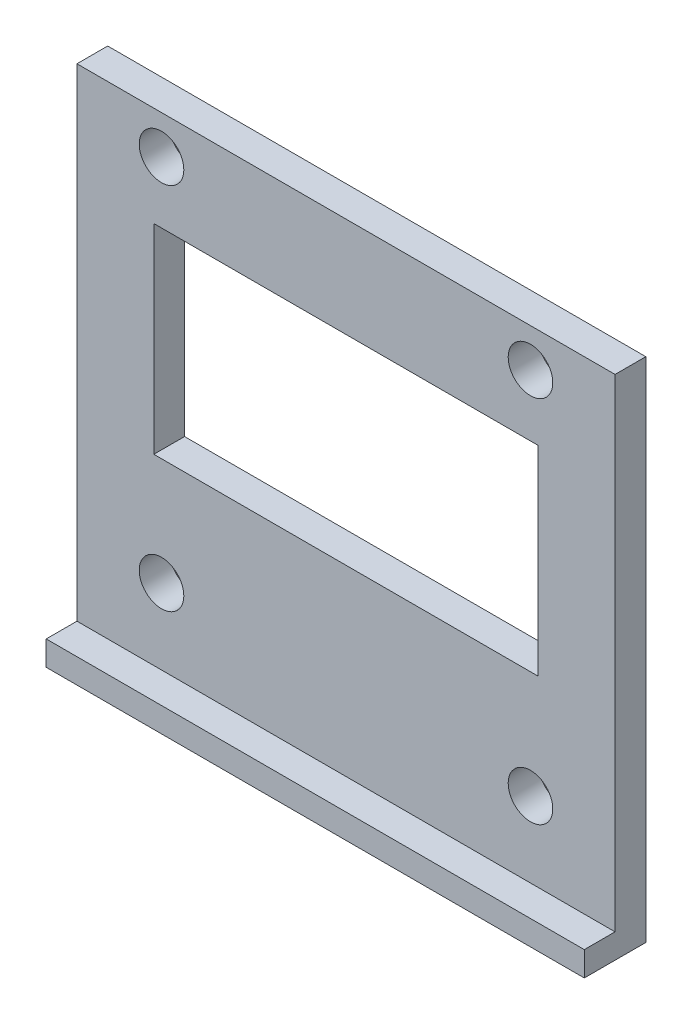
SolidWorks part; units mm, degrees
ref_plane "Front Plane" through (0, 0, 0) normal (0, 0, 1) x (1, 0, 0)
ref_plane "Top Plane" through (0, 0, 0) normal (0, 1, 0) x (1, 0, 0)
ref_plane "Right Plane" through (0, 0, 0) normal (1, 0, 0) x (0, 0, -1)
sketch "Sketch1" plane through (0, 0, 0) normal (0, 0, 1) x (1, 0, 0)
  line L1 (-13.5, -7.5) -> (13.5, -7.5) construction
  line L2 (-13.5, -7.5) -> (-13.5, 7.5) construction
  line L3 (-13.5, 7.5) -> (13.5, 7.5) construction
  line L4 (13.5, -7.5) -> (13.5, 7.5) construction
  line L5 (-13.5, -7.5) -> (13.5, 7.5) construction
  line L6 (-13.5, 7.5) -> (13.5, -7.5) construction
  line L7 (-14.5, -16) -> (14.5, -16)
  line L8 (-14.5, -16) -> (-14.5, 12)
  line L9 (-14.5, 12) -> (14.5, 12)
  line L10 (14.5, -16) -> (14.5, 12)
  line L11 (-12.5, -6.5) -> (12.5, -6.5)
  line L12 (-12.5, -6.5) -> (-12.5, 6.5)
  line L13 (-12.5, 6.5) -> (12.5, 6.5)
  line L14 (12.5, -6.5) -> (12.5, 6.5)
  line L15 (-12.5, -6.5) -> (12.5, 6.5) construction
  line L16 (-12.5, 6.5) -> (12.5, -6.5) construction
  point P0 (0, 0)
  point P10 (0, 0)
  dimension "D1" = 27
  dimension "D2" = 15
  dimension "D3" = 28
  dimension "D4" = 29
  dimension "D5" = 4.5
  dimension "D6" = 1
  dimension "D7" = 13
  dimension "D8" = 25
extrude "Boss-Extrude1" add sketch "Sketch1" along normal blind 2
sketch "Sketch2" plane through (0, 0, 2) normal (0, 0, 1) x (1, 0, 0)
  line L0 (-13.5, -20.4881) -> (-13.5, 20.4881) construction
  line L2 (0, 12) -> (0, -16) construction
  line L3 (14.5, 12) -> (-14.5, 12) construction
  line L4 (-14.5, -16) -> (14.5, -16) construction
  circle A0 centre (-12, 10.5) radius 1.5 construction
  circle A1 centre (-12, 10.5) radius 1.45
  circle A2 centre (-12, -13.5) radius 1.5 construction
  circle A3 centre (-12, -13.5) radius 1.45
  circle A4 centre (12, -13.5) radius 1.45
  circle A5 centre (12, 10.5) radius 1.45
  point P3 (-13.5, 0)
  dimension "D1" = 1.5
  dimension "D3" = 2.9
  dimension "D4" = 3
  dimension "D7" = 2.9
  dimension "D2" = 1.5
  dimension "D5" = 2.5
  dimension "D6" = 1.5
extrude "Cut-Extrude1" cut sketch "Sketch2" against normal through all
sketch "Sketch3" plane through (14.5, 0, 0) normal (1, 0, 0) x (0, 0, -1)
  line L1 (-4, -20) -> (0, -20)
  line L2 (0, -20) -> (0, -18.4)
  line L6 (0, -18.4) -> (0, -16)
  line L7 (0, -16) -> (-2, -16)
  line L8 (-2, -18.4) -> (-2, -16)
  line L9 (-2, -18.4) -> (-4, -18.4)
  line L10 (-4, -18.4) -> (-4, -20)
  dimension "D1" = 1.6
  dimension "D2" = 4
  dimension "D3" = 2.4
extrude "Boss-Extrude2" add sketch "Sketch3" against normal through all
sketch "Sketch5" plane through (0, 12, 0) normal (0, 1, 0) x (1, 0, 0)
  line L1 (-14.5, -2) -> (14.5, -2)
  line L2 (-14.5, -2) -> (-14.5, 0)
  line L3 (-14.5, 0) -> (14.5, 0)
  line L4 (14.5, -2) -> (14.5, 0)
extrude "Boss-Extrude3" add sketch "Sketch5" along normal blind 1
ref_plane "Plane1" through (-14.5, 0, 0) normal (-1, 0, 0) x (0, 0, 1)
sketch "Sketch6" plane through (-14.5, 0, 0) normal (-1, 0, 0) x (0, 0, 1)
  line L1 (0, -20) -> (2, -20)
  line L2 (0, -20) -> (0, 13)
  line L3 (0, 13) -> (2, 13)
  line L4 (2, -20) -> (2, 13)
  line L5 (2, -18.4) -> (4, -18.4)
  line L6 (2, -18.4) -> (2, -20)
  line L7 (2, -20) -> (4, -20)
  line L8 (4, -18.4) -> (4, -20)
extrude "Boss-Extrude4" add sketch "Sketch6" along normal blind 3 contours L1 L4 L3 L2 | L8 L5 L4 L7
ref_plane "Plane2" through (14.5, 0, 0) normal (1, 0, 0) x (0, 0, -1)
sketch "Sketch7" plane through (14.5, 0, 0) normal (1, 0, 0) x (0, 0, -1)
  line L1 (0, -20) -> (-2, -20)
  line L2 (0, -20) -> (0, 13)
  line L3 (0, 13) -> (-2, 13)
  line L4 (-2, -20) -> (-2, 13)
  line L5 (-2, -20) -> (-4, -20)
  line L6 (-2, -20) -> (-2, -18.4)
  line L7 (-2, -18.4) -> (-4, -18.4)
  line L8 (-4, -20) -> (-4, -18.4)
extrude "Boss-Extrude5" add sketch "Sketch7" along normal blind 3 contours L4 L1 L2 L3 | L8 L5 L4 L7
